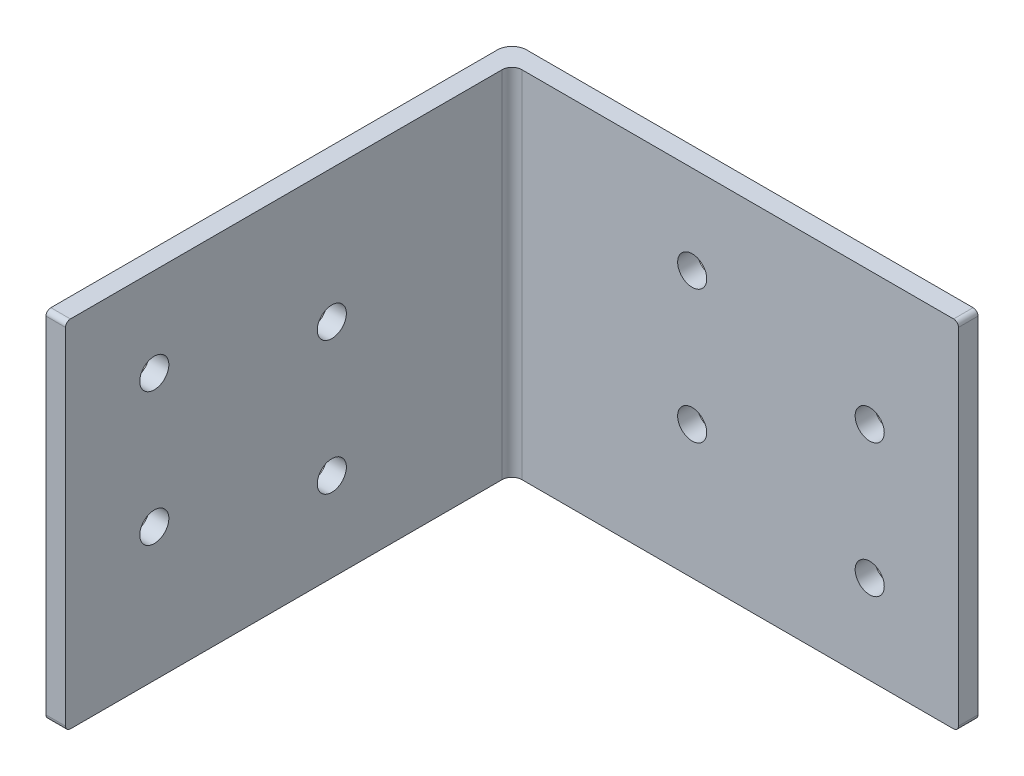
SolidWorks part; units mm, degrees
ref_plane "Front Plane" through (0, 0, 0) normal (0, 0, 1) x (1, 0, 0)
ref_plane "Top Plane" through (0, 0, 0) normal (0, 1, 0) x (1, 0, 0)
ref_plane "Right Plane" through (0, 0, 0) normal (1, 0, 0) x (0, 0, -1)
sketch "Sketch1" plane through (0, 0, 0) normal (0, 1, 0) x (1, 0, 0)
  line L0 (0, 0) -> (0, -65.278) construction
  line L1 (0, 0) -> (65.278, 0) construction
  line L2 (-1.397, -65.278) -> (1.397, -65.278) construction
  line L3 (65.278, -1.397) -> (65.278, 1.397) construction
  line L4 (65.278, 1.397) -> (-1.397, 1.397) construction
  line L5 (-1.397, 1.397) -> (-1.397, -65.278) construction
  line L6 (1.397, -65.278) -> (1.397, -1.397) construction
  line L7 (1.397, -1.397) -> (65.278, -1.397) construction
  point P7 (0, -65.278)
  point P10 (65.278, 0)
  dimension "Length (A)" = 66.675
  dimension "Length (B)" = 66.675
  dimension "Thickness" = 2.794
sketch "Sketch2" plane through (0, 0, 0) normal (1, 0, 0) x (0, 0, -1)
  line L0 (0, -25.4) -> (0, 25.4) construction
  line L1 (-52.578, -6.35) -> (-52.578, 12.7) construction
  line L3 (-27.178, -12.7) -> (-27.178, 6.35) construction
  line L4 (-29.2608, 6.35) -> (-25.0952, 6.35) construction
  point P5 (-52.578, -6.35)
  point P6 (0, 0)
  point P10 (-27.178, -3.175)
  point P13 (-27.178, 6.35)
  dimension "Length (C)" = 50.8
  dimension "Hole Diameter" = 4.1656
  dimension "Horizontal Center to Center" = 25.4
  dimension "Vertical Center to Center" = 19.05
  dimension "Hole Center" = 12.7
  dimension "Hole Center 2" = 12.7
  dimension "Hole Center 3" = 12.7
sketch "Sketch3" plane through (0, 0, 0) normal (0, 1, 0) x (1, 0, 0)
  line L0 (1.397, -1.397) -> (65.278, -1.397) construction
  line L1 (65.278, -1.397) -> (65.278, 1.397) construction
  line L2 (1.397, -65.278) -> (1.397, -1.397) construction
  line L3 (-1.397, -65.278) -> (1.397, -65.278) construction
  line L4 (-1.397, 1.397) -> (-1.397, -65.278) construction
  line L5 (65.278, 1.397) -> (-1.397, 1.397) construction
  line L6 (1.397, -1.397) -> (65.278, -1.397)
  line L7 (65.278, -1.397) -> (65.278, 1.397)
  line L8 (1.397, -65.278) -> (1.397, -1.397)
  line L9 (-1.397, -65.278) -> (1.397, -65.278)
  line L10 (-1.397, 1.397) -> (-1.397, -65.278)
  line L11 (65.278, 1.397) -> (-1.397, 1.397)
extrude "Boss-Extrude1" add sketch "Sketch3" along normal mid plane 50.8
fillet "Fillet1" radius 2.0955 1 edges at (-1.397, 0, -1.397)
fillet "Fillet2" radius 1.397 1 edges at (1.397, 0, 1.397)
fillet "Fillet3" radius 0.6985 4 edges at (65.278, -25.4, 0) (65.278, 25.4, 0) (0, -25.4, 65.278) (0, 25.4, 65.278)
sketch "Sketch4" plane through (1.397, 0, 0) normal (1, 0, 0) x (0, 0, -1)
  line L0 (-29.2608, 6.35) -> (-25.0952, 6.35) construction
  circle A0 centre (-52.578, -6.35) radius 2.0828
  circle A1 centre (-27.178, 6.35) radius 2.0828
  circle A2 centre (-27.178, -12.7) radius 2.0828
  circle A3 centre (-52.578, 12.7) radius 2.0828
extrude "Cut-Extrude1" cut sketch "Sketch4" against normal up to next
sketch "Sketch5" plane through (0, 0, 1.397) normal (0, 0, 1) x (1, 0, 0)
  line L2 (65.278, 24.7015) -> (65.278, -24.7015) construction
  circle A0 centre (27.178, 12.7) radius 2.0828
  circle A1 centre (27.178, -6.35) radius 2.0828
  circle A2 centre (52.578, -12.7) radius 2.0828
  circle A3 centre (52.578, 6.35) radius 2.0828
  dimension "D1" = 4.1656
  dimension "D2" = 12.7
  dimension "D3" = 25.4
extrude "Cut-Extrude2" cut sketch "Sketch5" against normal up to next
sketch "Sketch6" plane through (0, 0, 1.397) normal (0, 0, 1) x (1, 0, 0)
  line L0 (27.178, 12.7) -> (27.178, 14.7828) construction
  line L1 (27.178, 12.7) -> (28.6508, 14.1728) construction
  circle A0 centre (27.178, 12.7) radius 2.0828 construction
  point P7 (28.6508, 14.1728)
  point P8 (27.178, 14.7828)
  dimension "D1" = 45
ref_plane "Plane1" through (-1.397, 25.4, 0.6985) normal (0, -1, 0) x (-1, 0, 0)
sketch "Sketch8" plane through (-1.397, 0, 0) normal (-1, 0, 0) x (0, 0, 1)
  line L0 (0.6985, 0) -> (65.278, 0) construction
  line L1 (0.6985, 25.4) -> (0.6985, -25.4) construction
  line L2 (65.278, 24.7015) -> (65.278, -24.7015) construction
equation "\"D1@Boss-Extrude1\"=\"Length (C)@Sketch2\""
equation "\"D1@Fillet1\"=\"Thickness@Sketch1\"*.75"
equation "\"D1@Fillet2\"=\"Thickness@Sketch1\"*.5"
equation "\"D1@Fillet3\"=\"Thickness@Sketch1\"*.25"
equation "\"D1@Sketch5\"=\"Hole Diameter@Sketch2\""
equation "\"D2@Sketch5\"=\"Hole Center@Sketch2\""
equation "\"D3@Sketch5\"=\"Horizontal Center to Center@Sketch2\""
